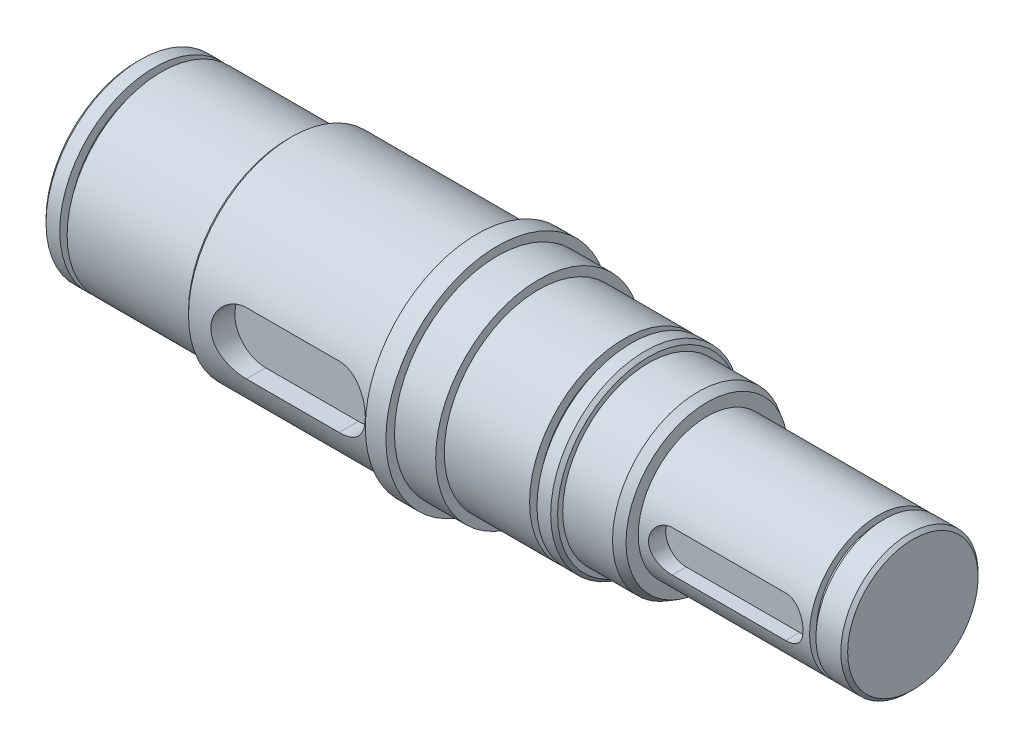
SolidWorks part; units mm, degrees
material "1.7225 (42CrMo4)"
ref_plane "Ebene vorne" through (0, 0, 0) normal (0, 0, 1) x (1, 0, 0)
ref_plane "Ebene oben" through (0, 0, 0) normal (0, 1, 0) x (1, 0, 0)
ref_plane "Ebene rechts" through (0, 0, 0) normal (1, 0, 0) x (0, 0, -1)
sketch "Skizze1" plane through (0, 0, 0) normal (0, 0, 1) x (1, 0, 0)
  line L0 (17.5895, 0) -> (-17.5895, 0) construction
  line L1 (168.1524, 0) -> (168.1524, 26.5)
  line L2 (169.1524, 27.5) -> (184.1524, 27.5)
  line L3 (168.1524, 26.5) -> (169.1524, 27.5)
  line L4 (184.1524, 27.5) -> (212.1524, 27.5)
  line L5 (212.1524, 27.5) -> (212.1524, 29)
  line L6 (213.1524, 30) -> (267.1524, 30)
  line L7 (212.1524, 29) -> (213.1524, 30)
  line L8 (267.1524, 30) -> (267.1524, 32.5)
  line L9 (267.1524, 32.5) -> (273.1524, 32.5)
  line L10 (273.1524, 32.5) -> (273.1524, 30)
  line L11 (273.1524, 30) -> (285.1524, 30)
  line L12 (285.1524, 30) -> (285.1524, 27.5)
  line L13 (285.1524, 27.5) -> (297.6524, 27.5)
  line L14 (297.6524, 27.5) -> (316.1524, 27.5)
  line L15 (297.6524, -28.9351) -> (297.6524, 58.108) construction
  line L16 (317.1524, 26.5) -> (317.1524, 25)
  line L17 (317.1524, 25) -> (331.6524, 25)
  line L18 (316.1524, 27.5) -> (317.1524, 26.5)
  line L19 (334.1524, 23.5566) -> (334.1524, 20)
  line L20 (334.1524, 20) -> (393.1524, 20)
  line L21 (331.6524, 25) -> (334.1524, 23.5566)
  line L22 (394.1524, 19) -> (394.1524, 0)
  line L23 (393.1524, 20) -> (394.1524, 19)
  line L24 (168.1524, 0) -> (394.1524, 0)
  point P4 (168.1524, 27.5)
  point P10 (212.1524, 30)
  point P20 (317.1524, 27.5)
  point P28 (394.1524, 20)
  point P29 (334.1524, 25)
  point P34 (168.1524, 0)
  point P54 (394.1524, 0)
  dimension "D1" = 27.5
  dimension "D2" = 16
  dimension "D3" = 28
  dimension "D4" = 30
  dimension "D5" = 55
  dimension "D8" = 32.5
  dimension "D9" = 6
  dimension "D10" = 30
  dimension "D11" = 27.5
  dimension "D12" = 12.5
  dimension "D13" = 113.5
  dimension "D14" = 19.5
  dimension "D15" = 17
  dimension "D16" = 2.5
  dimension "D18" = 30
  dimension "D19" = 25
  dimension "D20" = 20
  dimension "D21" = 60
  dimension "D22" = 1
  dimension "D23" = 45
  dimension "D24" = 394.1524
  dimension "D25" = 19
  dimension "D26" = 168.1524
  dimension "D27" = 26.5
revolve "Rotation17" add sketch "Skizze1" angle 360 about L24
ref_plane "Federnut Zahnrad" through (0, 0, 30) normal (0, 0, 1) x (1, 0, 0)
sketch "Skizze3" plane through (0, 0, 30) normal (0, 0, 1) x (1, 0, 0)
  line L0 (228.6524, 0) -> (255.6524, 0) construction
  line L2 (35.75, 0) -> (-35.75, 0) construction
  line L3 (228.6524, 9) -> (255.6524, 9)
  line L4 (228.6524, -9) -> (255.6524, -9)
  line L6 (267.1524, 30) -> (267.1524, -30) construction
  arc A0 (228.6524, 9) -> (228.6524, -9) centre (228.6524, 0) ccw
  arc A1 (255.6524, -9) -> (255.6524, 9) centre (255.6524, 0) ccw
  point P4 (242.1524, 0)
  point P10 (219.6524, 0)
  point P12 (264.6524, 0)
  dimension "D1" = 45
  dimension "D2" = 2.5
  dimension "D3" = 18
extrude "Schnitt-Linear austragen1" cut sketch "Skizze3" against normal blind 7
ref_plane "Federnut Riemenscheibe" through (0, 0, 20) normal (0, 0, 1) x (1, 0, 0)
sketch "Skizze4" plane through (0, 0, 20) normal (0, 0, 1) x (1, 0, 0)
  line L0 (35.75, 0) -> (-35.75, 0) construction
  line L1 (334.1524, -20) -> (334.1524, 20) construction
  line L2 (343.1524, 0) -> (376.1524, 0) construction
  line L3 (343.1524, 6) -> (376.1524, 6)
  line L4 (343.1524, -6) -> (376.1524, -6)
  arc A0 (343.1524, 6) -> (343.1524, -6) centre (343.1524, 0) ccw
  arc A1 (376.1524, -6) -> (376.1524, 6) centre (376.1524, 0) ccw
  point P0 (337.1524, 0)
  point P5 (343.1524, 0)
  point P6 (376.1524, 0)
  point P9 (359.6524, 0)
  dimension "D4" = 12
  dimension "D1" = 3
  dimension "D2" = 6
  dimension "D3" = 33
extrude "Schnitt-Linear austragen2" cut sketch "Skizze4" against normal blind 5
sketch "Skizze5" plane through (0, 0, 20) normal (0, 0, 1) x (1, 0, 0)
  line L1 (35.75, 0) -> (-35.75, 0) construction
  arc A1 (376.1524, -6) -> (376.1524, 6) centre (376.1524, 0) ccw construction
  point P0 (382.1524, 0)
  point P1 (384.1524, 0)
  dimension "D1" = 2
ref_plane "Ebene4" through (168.1524, 0, 0) normal (0, -1, 0) x (0, 0, 1)
sketch "Skizze7" plane through (168.1524, 0, 0) normal (0, -1, 0) x (0, 0, 1)
  line L0 (18.935, -216.925) -> (24, -216.925)
  line L1 (24, -216.925) -> (24, -215.075)
  line L2 (24, -215.075) -> (18.935, -215.075)
  line L3 (18.75, -215.26) -> (18.75, -216.74)
  line L4 (0, -50) -> (0, 50) construction
  arc A0 (18.75, -216.74) -> (18.935, -216.925) centre (18.935, -216.74) ccw
  arc A1 (18.75, -215.26) -> (18.935, -215.075) centre (18.935, -215.26) cw
  dimension "D1" = 0.185
  dimension "D2" = 0.185
  dimension "D3" = 18.75
  dimension "D4" = 24
  dimension "D5" = 383.2274
  dimension "D6" = 385.0774
ref_plane "Ebene5" through (168.1524, 0, 0) normal (0, -1, 0) x (0, 0, 1)
sketch "Skizze9" plane through (168.1524, 0, 0) normal (0, -1, 0) x (0, 0, 1)
  line L0 (18.935, -217.85) -> (24, -217.85)
  line L1 (24, -217.85) -> (24, -216)
  line L2 (24, -216) -> (18.935, -216)
  line L3 (18.75, -216.185) -> (18.75, -217.665)
  line L4 (0, -50) -> (0, 50) construction
  arc A0 (18.75, -217.665) -> (18.935, -217.85) centre (18.935, -217.665) ccw
  arc A1 (18.75, -216.185) -> (18.935, -216) centre (18.935, -216.185) cw
  dimension "D1" = 0.185
  dimension "D2" = 0.185
  dimension "D3" = 2
ref_plane "Sicherungsnut Lager" through (0, 0, 27.5) normal (0, 0, 1) x (1, 0, 0)
ref_plane "Ebene7" through (168.1524, 0, 0) normal (0, -1, 0) x (0, 0, 1)
ref_plane "Ebene8" through (168.1524, 0, 0) normal (0, -1, 0) x (0, 0, 1)
sketch "Skizze14" plane through (168.1524, 0, 0) normal (0, -1, 0) x (0, 0, 1)
  line L4 (0, -262.3218) -> (0, 50) construction
ref_plane "Ebene9" through (168.1524, 0, 0) normal (0, -1, 0) x (0, 0, 1)
sketch "Skizze16" plane through (168.1524, 0, 0) normal (0, -1, 0) x (0, 0, 1)
  line L0 (28.785, -7.15) -> (24.75, -7.15)
  line L1 (24.75, -7.15) -> (24.75, -5)
  line L2 (24.75, -5) -> (28.785, -5)
  line L3 (29, -5.215) -> (29, -6.935)
  line L4 (0, -50) -> (0, 50) construction
  line L5 (26.5, 0) -> (-26.5, 0) construction
  arc A0 (29, -6.935) -> (28.785, -7.15) centre (28.785, -6.935) cw
  arc A1 (29, -5.215) -> (28.785, -5) centre (28.785, -5.215) ccw
  dimension "D1" = 0.215
  dimension "D2" = 0.215
  dimension "D3" = 5
revolve "Nut für DIN 472 - 55 x 2, Sicherungsring für Bohrungen - Regelausf.1" cut sketch "Skizze16"
ref_plane "Ebene10" through (168.1524, 0, 0) normal (0, -1, 0) x (0, 0, 1)
sketch "Skizze18" plane through (168.1524, 0, 0) normal (0, -1, 0) x (0, 0, 1)
  line L0 (21.065, -217.75) -> (18, -217.75)
  line L1 (18, -217.75) -> (18, -215.9)
  line L2 (18, -215.9) -> (21.065, -215.9)
  line L3 (21.25, -216.085) -> (21.25, -217.565)
  line L4 (0, -50) -> (0, 50) construction
  arc A0 (21.25, -217.565) -> (21.065, -217.75) centre (21.065, -217.565) cw
  arc A1 (21.25, -216.085) -> (21.065, -215.9) centre (21.065, -216.085) ccw
  dimension "D1" = 0.185
  dimension "D2" = 0.185
  dimension "D3" = 51.75
revolve "Nut für DIN 472 - 40 x 1.75, Sicherungsring für Bohrungen - Regelausf.1" cut sketch "Skizze18" angle 360 about L4
ref_plane "Ebene11" through (168.1524, 0, 0) normal (0, -1, 0) x (0, 0, 1)
sketch "Skizze20" plane through (168.1524, 0, 0) normal (0, -1, 0) x (0, 0, 1)
  line L0 (28.785, -144) -> (24.75, -144)
  line L1 (24.75, -144) -> (24.75, -141.85)
  line L2 (24.75, -141.85) -> (28.785, -141.85)
  line L3 (29, -142.065) -> (29, -143.785)
  line L4 (0, -50) -> (0, 50) construction
  line L5 (-30, -117) -> (30, -117) construction
  arc A0 (29, -143.785) -> (28.785, -144) centre (28.785, -143.785) cw
  arc A1 (29, -142.065) -> (28.785, -141.85) centre (28.785, -142.065) ccw
  dimension "D1" = 0.215
  dimension "D2" = 0.215
  dimension "D3" = 2.15
  dimension "D4" = 27
revolve "Nut für DIN 472 - 55 x 2, Sicherungsring für Bohrungen - Regelausf.2" cut sketch "Skizze20" angle 360 about L4
